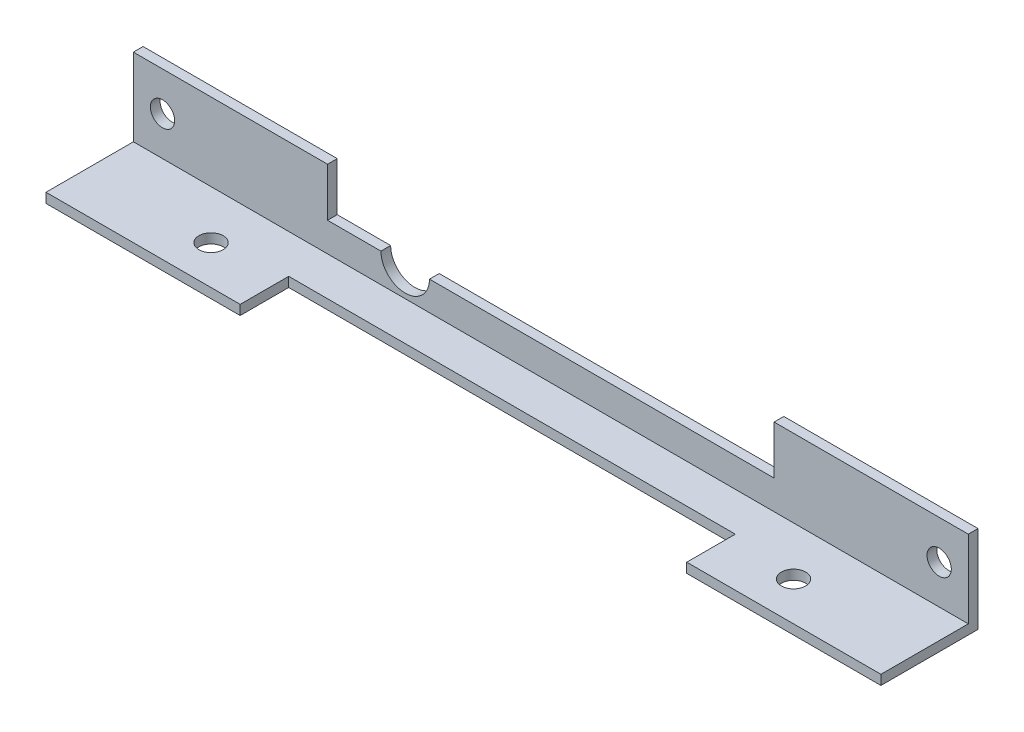
SolidWorks part; units mm, degrees
ref_plane "Front Plane" through (0, 0, 0) normal (0, 0, 1) x (1, 0, 0)
ref_plane "Top Plane" through (0, 0, 0) normal (0, 1, 0) x (1, 0, 0)
ref_plane "Right Plane" through (0, 0, 0) normal (1, 0, 0) x (0, 0, -1)
sketch "Esquisse1" plane through (0, 0, 0) normal (0, 1, 0) x (1, 0, 0)
  line L1 (-74.2569, 10.8716) -> (11.7431, 10.8716)
  line L2 (-74.2569, 10.8716) -> (-74.2569, 0.8716)
  line L3 (-74.2569, 0.8716) -> (11.7431, 0.8716)
  line L4 (11.7431, 10.8716) -> (11.7431, 0.8716)
  dimension "D1" = 86
  dimension "D2" = 10
extrude "Boss.-Extru.1" add sketch "Esquisse1" along normal blind 1
sketch "Esquisse2" plane through (0, 1, 0) normal (0, 1, 0) x (1, 0, 0)
  line L0 (11.7431, 0.8716) -> (11.7431, 10.8716) construction
  line L1 (-74.2569, 10.8716) -> (11.7431, 10.8716)
  line L2 (-74.2569, 10.8716) -> (-74.2569, 9.8716)
  line L3 (-74.2569, 9.8716) -> (11.7431, 9.8716)
  line L4 (11.7431, 10.8716) -> (11.7431, 9.8716)
  dimension "D1" = 1
extrude "Boss.-Extru.2" add sketch "Esquisse2" along normal blind 8
sketch "Esquisse3" plane through (0, 0, -9.8716) normal (0, 0, 1) x (1, 0, 0)
  line L0 (11.7431, 9) -> (11.7431, 1) construction
  line L1 (-74.2569, 9) -> (11.7431, 9) construction
  line L2 (-74.2569, 9) -> (-74.2569, 1) construction
  circle A0 centre (8.7431, 5) radius 1.25
  circle A1 centre (-71.2569, 5) radius 1.25
  dimension "D1" = 3
  dimension "D3" = 3
  dimension "D2" = 4
  dimension "D4" = 4
extrude "Enlèv. mat.-Extru.1" cut sketch "Esquisse3" against normal blind 10
sketch "Esquisse4" plane through (0, 1, 0) normal (0, 1, 0) x (1, 0, 0)
  line L0 (-74.2569, 9.8716) -> (-74.2569, 0.8716) construction
  line L1 (-74.2569, 0.8716) -> (11.7431, 0.8716) construction
  line L4 (11.7431, 0.8716) -> (11.7431, 9.8716) construction
  circle A0 centre (-61.2569, 4.8716) radius 1.25
  circle A1 centre (-1.2569, 4.8716) radius 1.25
  dimension "D1" = 13
  dimension "D3" = 4
  dimension "D2" = 4
  dimension "D4" = 13
extrude "Enlèv. mat.-Extru.2" cut sketch "Esquisse4" against normal blind 10
sketch "Esquisse5" plane through (0, 1, 0) normal (0, 1, 0) x (1, 0, 0)
  line L0 (-74.2569, 0.8716) -> (11.7431, 0.8716) construction
  line L1 (-54.2569, 5.8716) -> (-8.2569, 5.8716)
  line L2 (-54.2569, 5.8716) -> (-54.2569, 0.8716)
  line L3 (-54.2569, 0.8716) -> (-8.2569, 0.8716)
  line L4 (-8.2569, 5.8716) -> (-8.2569, 0.8716)
  line L5 (-74.2569, 9.8716) -> (-74.2569, 0.8716) construction
  line L6 (11.7431, 0.8716) -> (11.7431, 9.8716) construction
  point P8 (-74.2569, 5.3716)
  dimension "D1" = 20
  dimension "D2" = 20
  dimension "D3" = 5
extrude "Enlèv. mat.-Extru.3" cut sketch "Esquisse5" against normal blind 10
sketch "Esquisse6" plane through (0, 0, -9.8716) normal (0, 0, 1) x (1, 0, 0)
  line L0 (-74.2569, 9) -> (11.7431, 9) construction
  line L1 (-54.2569, 9) -> (-8.2569, 9)
  line L2 (-54.2569, 9) -> (-54.2569, 4)
  line L3 (-54.2569, 4) -> (-8.2569, 4)
  line L4 (-8.2569, 9) -> (-8.2569, 4)
  line L5 (11.7431, 9) -> (11.7431, 1) construction
  line L6 (-74.2569, 9) -> (-74.2569, 1) construction
  dimension "D1" = 5
  dimension "D2" = 20
  dimension "D3" = 20
extrude "Enlèv. mat.-Extru.4" cut sketch "Esquisse6" against normal blind 10
sketch "Esquisse8" plane through (0, 0, -9.8716) normal (0, 0, 1) x (1, 0, 0)
  line L0 (-54.2569, 4) -> (-8.2569, 4) construction
  line L1 (-74.2569, 9) -> (-74.2569, 1) construction
  line L2 (-74.2569, 9) -> (-54.2569, 9) construction
  circle A0 centre (-46.2569, 4) radius 2.5
  dimension "D1" = 5
  dimension "D2" = 28
  dimension "D3" = 5
extrude "Enlèv. mat.-Extru.5" cut sketch "Esquisse8" against normal blind 10
